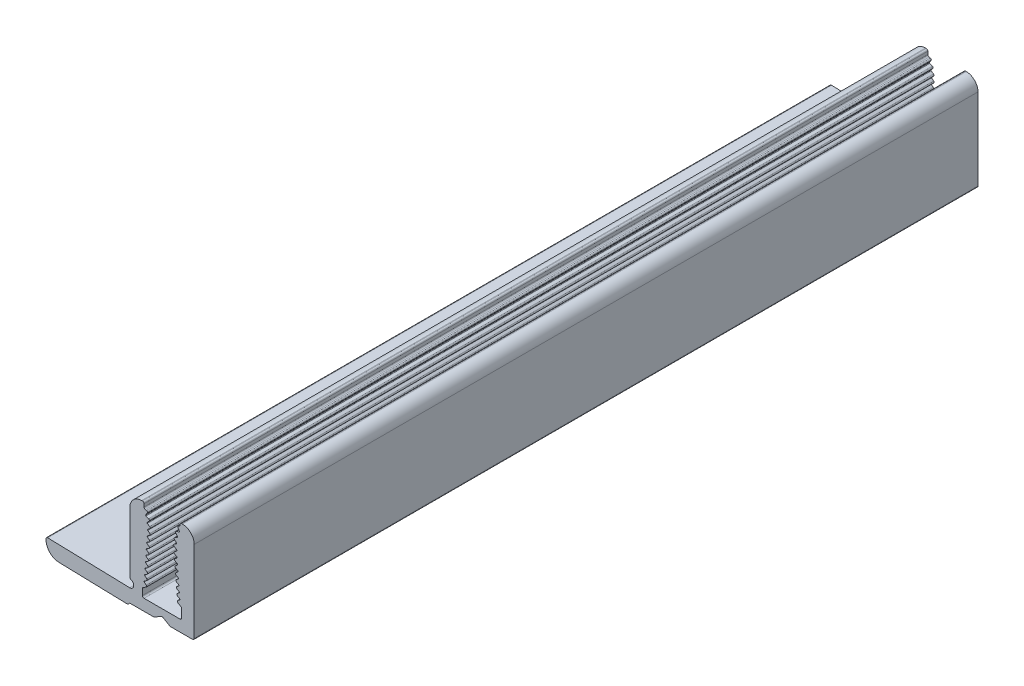
SolidWorks part; units mm, degrees
material "АД31 ГОСТ 4784-97"
ref_plane "Спереди" through (0, 0, 0) normal (0, 0, 1) x (1, 0, 0)
ref_plane "Сверху" through (0, 0, 0) normal (0, 1, 0) x (1, 0, 0)
ref_plane "Справа" through (0, 0, 0) normal (1, 0, 0) x (0, 0, -1)
sketch "Эскиз1" plane through (0, 0, 0) normal (0, 0, 1) x (1, 0, 0)
  line L7 (311.0909, 325.0503) -> (319.788, 324.8102)
  line L8 (319.935, 324.8687) -> (320.1312, 325.065)
  line L9 (320.1312, 325.065) -> (323.2019, 325.065)
  line L10 (323.2019, 325.065) -> (324.1411, 325.6072)
  line L11 (324.3411, 325.6072) -> (325.2804, 325.065)
  line L12 (325.2804, 325.065) -> (328.1411, 325.065)
  line L13 (328.3411, 325.265) -> (328.3411, 335.6601)
  line L14 (326.8411, 337.1601) -> (326.751, 337.1601)
  line L15 (326.551, 336.9601) -> (326.551, 336.8985)
  line L16 (326.2767, 336.4828) -> (326.4473, 336.1731)
  line L17 (326.4041, 336.0663) -> (326.0666, 335.9622)
  line L18 (325.993, 335.7292) -> (326.2096, 335.4502)
  line L19 (326.1836, 335.3379) -> (325.8662, 335.1823)
  line L20 (325.8348, 334.9361) -> (326.0875, 334.7192)
  line L21 (326.0791, 334.6002) -> (325.7981, 334.4213)
  line L22 (325.7944, 334.1731) -> (326.0835, 333.9768)
  line L23 (326.0907, 333.7978) -> (325.8346, 333.5918)
  line L24 (325.8536, 333.3473) -> (326.1417, 333.1815)
  line L25 (326.1512, 333.0593) -> (325.8922, 332.851)
  line L26 (325.9112, 332.6064) -> (326.1993, 332.4407)
  line L27 (326.2088, 332.3184) -> (325.9498, 332.1101)
  line L28 (325.9688, 331.8656) -> (326.2569, 331.6998)
  line L29 (326.2664, 331.5776) -> (326.0074, 331.3693)
  line L30 (326.0264, 331.1247) -> (326.3145, 330.959)
  line L31 (326.324, 330.8367) -> (326.065, 330.6284)
  line L32 (326.084, 330.3839) -> (326.3721, 330.2182)
  line L33 (326.3816, 330.0959) -> (326.1226, 329.8876)
  line L34 (326.1417, 329.643) -> (326.4297, 329.4773)
  line L35 (326.4392, 329.355) -> (326.1802, 329.1468)
  line L36 (326.1993, 328.9022) -> (326.4873, 328.7365)
  line L37 (326.4968, 328.6142) -> (326.2379, 328.4059)
  line L38 (326.2569, 328.1614) -> (326.6409, 327.9404)
  line L39 (326.7411, 327.7671) -> (326.7411, 326.7101)
  line L40 (326.5411, 326.5101) -> (321.9411, 326.5101)
  line L41 (321.7411, 326.7101) -> (321.7411, 327.4865)
  line L42 (321.8414, 327.6599) -> (322.2026, 327.8677)
  line L43 (322.2216, 328.1122) -> (321.9626, 328.3205)
  line L44 (321.9721, 328.4428) -> (322.2602, 328.6085)
  line L45 (322.2792, 328.8531) -> (322.0202, 329.0613)
  line L46 (322.0297, 329.1836) -> (322.3178, 329.3494)
  line L47 (322.3368, 329.5939) -> (322.0778, 329.8022)
  line L48 (322.0873, 329.9245) -> (322.3754, 330.0902)
  line L49 (322.3944, 330.3348) -> (322.1354, 330.543)
  line L50 (322.1449, 330.6653) -> (322.433, 330.831)
  line L51 (322.452, 331.0756) -> (322.193, 331.2839)
  line L52 (322.2025, 331.4061) -> (322.4906, 331.5719)
  line L53 (322.5096, 331.8164) -> (322.2506, 332.0247)
  line L54 (322.2601, 332.147) -> (322.5482, 332.3127)
  line L55 (322.5672, 332.5573) -> (322.3082, 332.7656)
  line L56 (322.3177, 332.8878) -> (322.6058, 333.0536)
  line L57 (322.6248, 333.2981) -> (322.3658, 333.5064)
  line L58 (322.3753, 333.6287) -> (322.6634, 333.7944)
  line L59 (322.6782, 334.0422) -> (322.4114, 334.2415)
  line L60 (322.4117, 334.3608) -> (322.6799, 334.5584)
  line L61 (322.667, 334.8062) -> (322.362, 334.985)
  line L62 (322.3444, 335.0988) -> (322.5811, 335.3609)
  line L63 (322.5251, 335.5988) -> (322.1963, 335.7277)
  line L64 (322.1612, 335.8375) -> (322.3543, 336.1336)
  line L65 (322.2553, 336.3611) -> (322.1069, 336.3869)
  line L66 (321.9411, 336.584) -> (321.9411, 336.9601)
  line L67 (321.7411, 337.1601) -> (321.6411, 337.1601)
  line L68 (320.1411, 335.6601) -> (320.1411, 327.928)
  line L69 (320.1174, 326.7604) -> (309.6433, 327.0495)
  line L70 (309.4378, 326.8496) -> (309.4378, 326.7497)
  arc A1 (309.4378, 326.7497) -> (311.0909, 325.0503) centre (311.1378, 326.7497) ccw
  arc A2 (319.788, 324.8102) -> (319.935, 324.8687) centre (319.7936, 325.0101) ccw
  arc A3 (324.3411, 325.6072) -> (324.1411, 325.6072) centre (324.2411, 325.434) ccw
  arc A4 (328.1411, 325.065) -> (328.3411, 325.265) centre (328.1411, 325.265) ccw
  arc A5 (328.3411, 335.6601) -> (326.8411, 337.1601) centre (326.8411, 335.6601) ccw
  arc A6 (326.751, 337.1601) -> (326.551, 336.9601) centre (326.751, 336.9601) ccw
  arc A7 (326.3831, 336.7011) -> (326.551, 336.8985) centre (326.351, 336.8985) ccw
  arc A8 (326.3831, 336.7011) -> (326.2767, 336.4828) centre (326.4069, 336.5545) ccw
  arc A9 (326.4041, 336.0663) -> (326.4473, 336.1731) centre (326.3822, 336.1373) ccw
  arc A10 (326.0666, 335.9622) -> (325.993, 335.7292) centre (326.1104, 335.8203) ccw
  arc A11 (326.1836, 335.3379) -> (326.2096, 335.4502) centre (326.1509, 335.4046) ccw
  arc A12 (325.8662, 335.1823) -> (325.8348, 334.9361) centre (325.9316, 335.0489) ccw
  arc A13 (326.0791, 334.6002) -> (326.0875, 334.7192) centre (326.0392, 334.6629) ccw
  arc A14 (325.7981, 334.4213) -> (325.7944, 334.1731) centre (325.8779, 334.296) ccw
  arc A15 (326.0907, 333.7978) -> (326.0835, 333.9768) centre (326.0209, 333.8846) ccw
  arc A16 (325.8346, 333.5918) -> (325.8536, 333.3473) centre (325.9277, 333.476) ccw
  arc A17 (326.1512, 333.0593) -> (326.1417, 333.1815) centre (326.1046, 333.1171) ccw
  arc A18 (325.8922, 332.851) -> (325.9112, 332.6064) centre (325.9853, 332.7352) ccw
  arc A19 (326.2088, 332.3184) -> (326.1993, 332.4407) centre (326.1622, 332.3763) ccw
  arc A20 (325.9498, 332.1101) -> (325.9688, 331.8656) centre (326.0429, 331.9944) ccw
  arc A21 (326.2664, 331.5776) -> (326.2569, 331.6998) centre (326.2199, 331.6355) ccw
  arc A22 (326.0074, 331.3693) -> (326.0264, 331.1247) centre (326.1005, 331.2535) ccw
  arc A23 (326.324, 330.8367) -> (326.3145, 330.959) centre (326.2775, 330.8946) ccw
  arc A24 (326.065, 330.6284) -> (326.084, 330.3839) centre (326.1581, 330.5127) ccw
  arc A25 (326.3816, 330.0959) -> (326.3721, 330.2182) centre (326.3351, 330.1538) ccw
  arc A26 (326.1226, 329.8876) -> (326.1417, 329.643) centre (326.2157, 329.7718) ccw
  arc A27 (326.4392, 329.355) -> (326.4297, 329.4773) centre (326.3927, 329.4129) ccw
  arc A28 (326.1802, 329.1468) -> (326.1993, 328.9022) centre (326.2734, 329.031) ccw
  arc A29 (326.4968, 328.6142) -> (326.4873, 328.7365) centre (326.4503, 328.6721) ccw
  arc A30 (326.2379, 328.4059) -> (326.2569, 328.1614) centre (326.331, 328.2901) ccw
  arc A31 (326.7411, 327.7671) -> (326.6409, 327.9404) centre (326.5411, 327.7671) ccw
  arc A32 (326.5411, 326.5101) -> (326.7411, 326.7101) centre (326.5411, 326.7101) ccw
  arc A33 (321.7411, 326.7101) -> (321.9411, 326.5101) centre (321.9411, 326.7101) ccw
  arc A34 (321.8414, 327.6599) -> (321.7411, 327.4865) centre (321.9411, 327.4865) ccw
  arc A35 (322.2026, 327.8677) -> (322.2216, 328.1122) centre (322.1285, 327.9964) ccw
  arc A36 (321.9721, 328.4428) -> (321.9626, 328.3205) centre (322.0091, 328.3784) ccw
  arc A37 (322.2602, 328.6085) -> (322.2792, 328.8531) centre (322.1861, 328.7373) ccw
  arc A38 (322.0297, 329.1836) -> (322.0202, 329.0613) centre (322.0667, 329.1192) ccw
  arc A39 (322.3178, 329.3494) -> (322.3368, 329.5939) centre (322.2437, 329.4781) ccw
  arc A40 (322.0873, 329.9245) -> (322.0778, 329.8022) centre (322.1244, 329.8601) ccw
  arc A41 (322.3754, 330.0902) -> (322.3944, 330.3348) centre (322.3013, 330.219) ccw
  arc A42 (322.1449, 330.6653) -> (322.1354, 330.543) centre (322.182, 330.6009) ccw
  arc A43 (322.433, 330.831) -> (322.452, 331.0756) centre (322.3589, 330.9598) ccw
  arc A44 (322.2025, 331.4061) -> (322.193, 331.2839) centre (322.2396, 331.3418) ccw
  arc A45 (322.4906, 331.5719) -> (322.5096, 331.8164) centre (322.4165, 331.7007) ccw
  arc A46 (322.2601, 332.147) -> (322.2506, 332.0247) centre (322.2972, 332.0826) ccw
  arc A47 (322.5482, 332.3127) -> (322.5672, 332.5573) centre (322.4741, 332.4415) ccw
  arc A48 (322.3177, 332.8878) -> (322.3082, 332.7656) centre (322.3548, 332.8234) ccw
  arc A49 (322.6058, 333.0536) -> (322.6248, 333.2981) centre (322.5317, 333.1823) ccw
  arc A50 (322.3753, 333.6287) -> (322.3658, 333.5064) centre (322.4124, 333.5643) ccw
  arc A51 (322.6634, 333.7944) -> (322.6782, 334.0422) centre (322.5893, 333.9232) ccw
  arc A52 (322.4117, 334.3608) -> (322.4114, 334.2415) centre (322.4558, 334.301) ccw
  arc A53 (322.6799, 334.5584) -> (322.667, 334.8062) centre (322.5918, 334.678) ccw
  arc A54 (322.3444, 335.0988) -> (322.362, 334.985) centre (322.3996, 335.049) ccw
  arc A55 (322.5811, 335.3609) -> (322.5251, 335.5988) centre (322.4709, 335.4605) ccw
  arc A56 (322.1612, 335.8375) -> (322.1963, 335.7277) centre (322.2234, 335.7969) ccw
  arc A57 (322.3543, 336.1336) -> (322.2553, 336.3611) centre (322.2298, 336.2148) ccw
  arc A58 (321.9411, 336.584) -> (322.1069, 336.3869) centre (322.1411, 336.584) ccw
  arc A59 (321.9411, 336.9601) -> (321.7411, 337.1601) centre (321.7411, 336.9601) ccw
  arc A60 (321.6411, 337.1601) -> (320.1411, 335.6601) centre (321.6411, 335.6601) ccw
  arc A61 (320.1411, 327.928) -> (320.2812, 327.7372) centre (320.3411, 327.928) ccw
  arc A62 (320.1174, 326.7604) -> (320.2812, 327.7372) centre (320.1312, 327.2602) ccw
  arc A63 (309.6433, 327.0495) -> (309.4378, 326.8496) centre (309.6378, 326.8496) ccw
extrude "Бобышка-Вытянуть1" add sketch "Эскиз1" along normal blind 100
